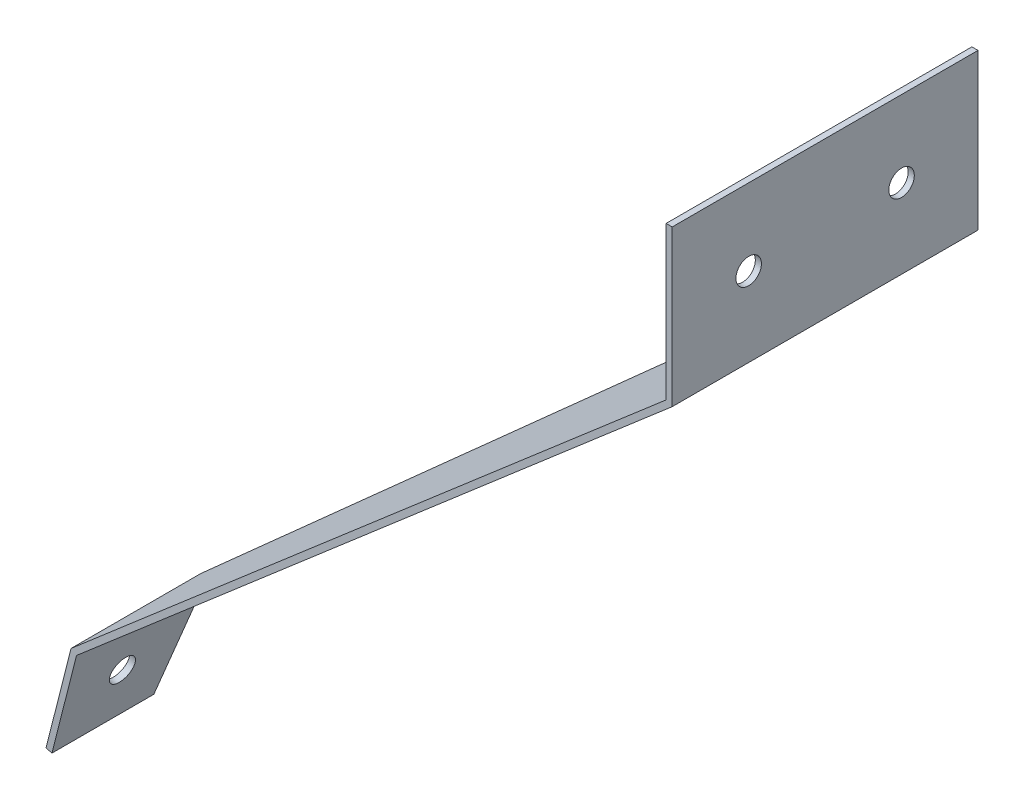
SolidWorks part; units mm, degrees
material "6061-T6 (SS)"
ref_plane "Front Plane" through (0, 0, 0) normal (0, 0, 1) x (1, 0, 0)
ref_plane "Top Plane" through (0, 0, 0) normal (0, 1, 0) x (1, 0, 0)
ref_plane "Right Plane" through (0, 0, 0) normal (1, 0, 0) x (0, 0, -1)
sketch "Sketch1" plane through (0, 0, 0) normal (0, 0, 1) x (1, 0, 0)
  line L0 (0, 0) -> (0, 38.1)
  line L1 (0, 0) -> (-148.2978, -127.7815)
  line L2 (-148.2978, -127.7815) -> (-154.5501, -152.4)
  line L3 (-148.2978, -127.7815) -> (-143.653, -109.4927) construction
  line L4 (1.524, -0.6985) -> (1.524, 38.1)
  line L5 (1.524, -0.6985) -> (-146.9389, -128.6224)
  line L6 (-146.9389, -128.6224) -> (-153.073, -152.7751)
  line L7 (-154.5501, -152.4) -> (-153.073, -152.7751)
  line L8 (1.524, 38.1) -> (0, 38.1)
  dimension "D1" = 130.75
  dimension "D2" = 35
  dimension "D3" = 25.4
  dimension "D4" = 38.1
  dimension "D5" = 190.5
  dimension "D6" = 1.524
extrude "Boss-Extrude1" add sketch "Sketch1" along normal blind 76.2 contours L1 L2 L7 L6 L5 L4 L8 L0
sketch "Sketch2" plane through (-108.8262, 27.6383, 0) normal (-0.9692, 0.2462, 0) x (0, 0, 1)
  line L0 (0, -185.7538) -> (50.8, -185.7538)
  line L1 (76.2, -185.7538) -> (0, -185.7538) construction
  line L2 (50.8, -185.7538) -> (0, 0)
  line L3 (0, 0) -> (0, -185.7538)
  dimension "D1" = 50.8
extrude "Cut-Extrude1" cut sketch "Sketch2" against normal through all
sketch "Sketch3" plane through (-108.8262, 27.6383, 0) normal (-0.9692, 0.2462, 0) x (0, 0, 1)
  line L0 (50.8, -185.7538) -> (76.2, -185.7538) construction
  line L1 (43.8536, -160.3538) -> (76.2, -160.3538) construction
  line L2 (60.0268, -160.3538) -> (63.5, -185.7538) construction
  circle A0 centre (61.7634, -173.0538) radius 3.175
  dimension "D1" = 6.35
extrude "Cut-Extrude2" cut sketch "Sketch3" against normal through all
sketch "Sketch4" plane through (0, 0, 0) normal (-1, 0, 0) x (0, 0, 1)
  line L0 (0, 38.1) -> (76.2, 38.1) construction
  line L1 (38.1, 38.1) -> (38.1, 0) construction
  line L2 (76.2, 0) -> (0, 0) construction
  line L3 (38.1, 19.05) -> (0, 19.05) construction
  line L4 (0, 0) -> (0, 38.1) construction
  line L5 (38.1, 19.05) -> (76.2, 19.05) construction
  line L6 (76.2, 0) -> (76.2, 38.1) construction
  circle A0 centre (19.05, 19.05) radius 3.175
  circle A1 centre (57.15, 19.05) radius 3.175
  dimension "D1" = 6.35
  dimension "D2" = 6.35
extrude "Cut-Extrude3" cut sketch "Sketch4" against normal through all
